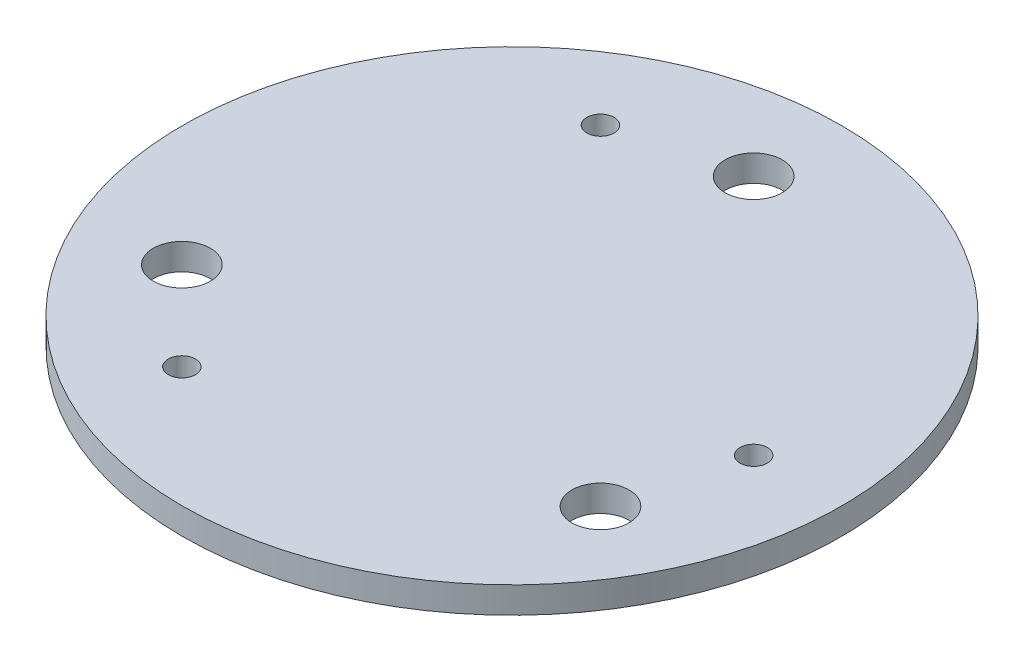
SolidWorks part; units mm, degrees
ref_plane "Front Plane" through (0, 0, 0) normal (0, 0, 1) x (1, 0, 0)
ref_plane "Top Plane" through (0, 0, 0) normal (0, 1, 0) x (1, 0, 0)
ref_plane "Right Plane" through (0, 0, 0) normal (1, 0, 0) x (0, 0, -1)
sketch "Sketch1" plane through (0, 0, 0) normal (0, 1, 0) x (1, 0, 0)
  line L1 (55, 0) -> (-27.5, 47.6314) construction
  line L2 (-27.5, 47.6314) -> (-27.5, -47.6314) construction
  line L3 (-27.5, -47.6314) -> (55, 0) construction
  line L4 (0, 0) -> (0, 55) construction
  line L6 (0, 55) -> (-47.6314, -27.5) construction
  line L7 (-47.6314, -27.5) -> (47.6314, -27.5) construction
  line L8 (47.6314, -27.5) -> (0, 55) construction
  circle A0 centre (0, 0) radius 75
  circle A1 centre (0, 0) radius 55 construction
  circle A2 centre (0, 0) radius 27.5 construction
  circle A3 centre (0, 0) radius 27.5 construction
  circle A4 centre (0, 55) radius 6.5
  circle A5 centre (-47.6314, -27.5) radius 6.5
  circle A6 centre (47.6314, -27.5) radius 6.5
  circle A7 centre (-27.5, 47.6314) radius 3.1
  circle A8 centre (55, 0) radius 3.1
  circle A9 centre (-27.5, -47.6314) radius 3.1
  dimension "D1" = 110
  dimension "D2" = 150
extrude "Boss-Extrude1" add sketch "Sketch1" along normal blind 6 contours A0 A6 A5 A4
